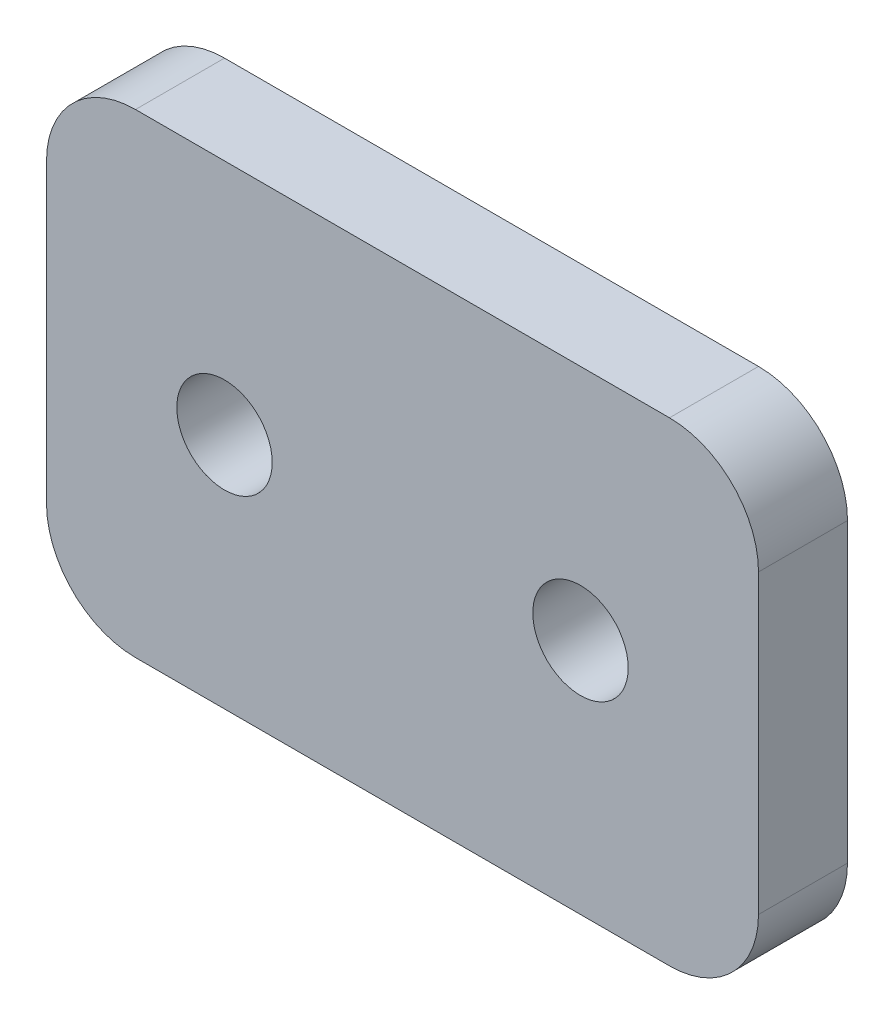
SolidWorks part; units mm, degrees
material "6061-T6 (SS)"
ref_plane "Front Plane" through (0, 0, 0) normal (0, 0, 1) x (1, 0, 0)
ref_plane "Top Plane" through (0, 0, 0) normal (0, 1, 0) x (1, 0, 0)
ref_plane "Right Plane" through (0, 0, 0) normal (1, 0, 0) x (0, 0, -1)
sketch "Sketch2" plane through (0, 0, 0) normal (0, 0, 1) x (1, 0, 0)
  line L1 (0, 0) -> (38.1, 0)
  line L2 (0, 0) -> (0, 25.4)
  line L3 (0, 25.4) -> (38.1, 25.4)
  line L4 (38.1, 0) -> (38.1, 25.4)
  circle A4 centre (9.525, 12.7) radius 2.5527
  circle A5 centre (28.575, 12.7) radius 2.5527
  point P12 (0, 12.7)
  dimension "D3" = 19.05
  dimension "D4" = 5.1054
  dimension "D1" = 25.4
  dimension "D2" = 38.1
  dimension ".375" = 9.525
extrude "Boss-Extrude1" add sketch "Sketch2" along normal blind 4.7625
fillet "Fillet1" radius 4.7625 4 edges at (0, 25.4, 2.3813) (0, 0, 2.3813) (38.1, 0, 2.3813) (38.1, 25.4, 2.3813)
